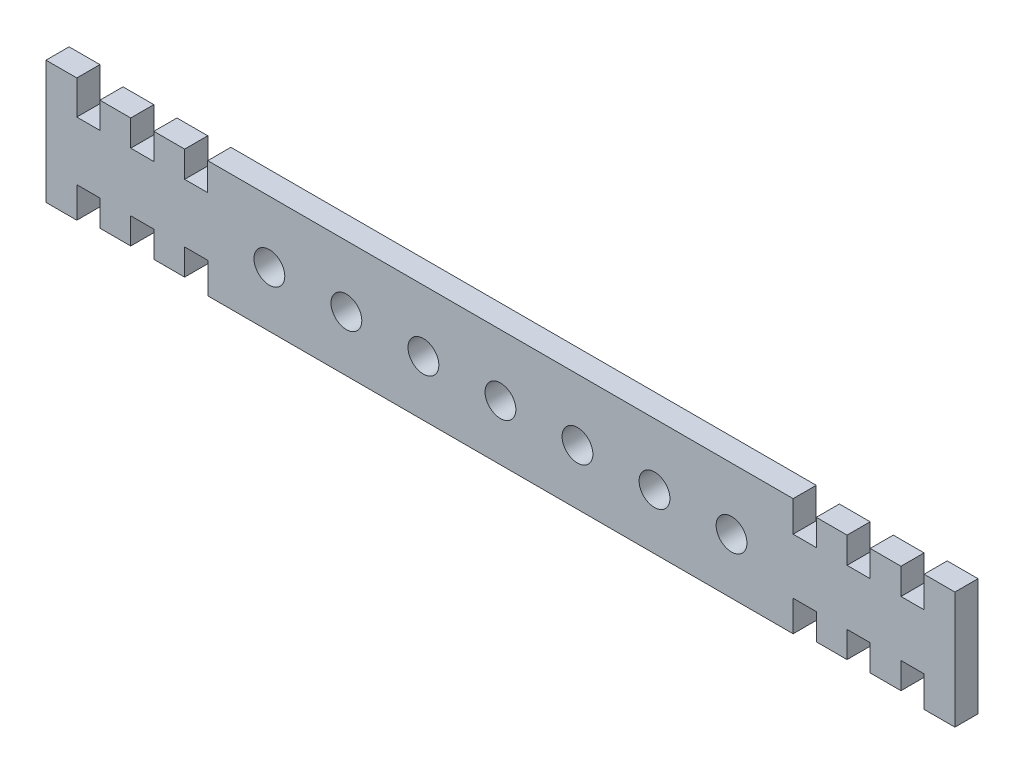
SolidWorks part; units mm, degrees
ref_plane "前视基准面" through (0, 0, 0) normal (0, 0, 1) x (1, 0, 0)
ref_plane "上视基准面" through (0, 0, 0) normal (0, 1, 0) x (1, 0, 0)
ref_plane "右视基准面" through (0, 0, 0) normal (1, 0, 0) x (0, 0, -1)
other "Configuration Table"
sketch "草图1" plane through (0, 0, 0) normal (0, 0, 1) x (1, 0, 0)
  line L0 (0, 0) -> (27.0318, 0) construction
  line L1 (0, -1.1987) -> (0, -17.6851) construction
  line L2 (-19.0005, 4) -> (18.9995, 4)
  line L37 (-19.0005, 4) -> (-19.0005, 2.2)
  line L38 (18.9995, 4) -> (18.9995, 2)
  line L39 (18.9995, 2) -> (20.5, 2)
  line L40 (20.5, 2) -> (20.5, 3.7)
  line L41 (20.5, 3.7) -> (22.4996, 3.7)
  line L42 (22.4996, 3.7) -> (22.4996, 2)
  line L43 (22.4996, 2) -> (24.0001, 2)
  line L44 (24.0001, 2) -> (24.0001, 3.7)
  line L45 (24.0001, 3.7) -> (25.9996, 3.7)
  line L46 (25.9996, 3.7) -> (25.9996, 2)
  line L48 (25.9996, 2) -> (27.5001, 2)
  line L49 (27.5001, 2) -> (27.5001, 4)
  line L50 (27.5001, 4) -> (29.4997, 4)
  line L51 (29.4997, 4) -> (29.4997, -3.6)
  line L54 (27.5, -3.6) -> (29.4997, -3.6)
  line L55 (27.5, -1.6) -> (27.5, -3.6)
  line L56 (26, -1.6) -> (27.5, -1.6)
  line L57 (26, -3.3) -> (26, -1.6)
  line L58 (24, -3.3) -> (26, -3.3)
  line L59 (24, -1.6) -> (24, -3.3)
  line L60 (22.5, -1.6) -> (24, -1.6)
  line L61 (22.5, -3.3) -> (22.5, -1.6)
  line L62 (20.5, -3.3) -> (22.5, -3.3)
  line L63 (20.5, -1.6) -> (20.5, -3.3)
  line L64 (19, -1.6) -> (20.5, -1.6)
  line L65 (19, -3.6) -> (19, -1.6)
  line L66 (-19, -3.6) -> (-19, -1.6)
  line L67 (-19, -1.6) -> (-20.5, -1.6)
  line L68 (-20.5, -1.6) -> (-20.5, -3.3)
  line L69 (-20.5, -3.3) -> (-22.5, -3.3)
  line L70 (-22.5, -3.3) -> (-22.5, -1.6)
  line L71 (-22.5, -1.6) -> (-24, -1.6)
  line L72 (-24, -1.6) -> (-24, -3.3)
  line L73 (-24, -3.3) -> (-26, -3.3)
  line L74 (-26, -3.3) -> (-26, -1.6)
  line L75 (-26, -1.6) -> (-27.5, -1.6)
  line L76 (-27.5, -1.6) -> (-27.5, -3.6)
  line L77 (-27.5, -3.6) -> (-29.5, -3.6)
  line L78 (-29.5, 4.4) -> (-29.5, -3.6)
  line L79 (-27.5, 4.4) -> (-29.5, 4.4)
  line L80 (-27.5, 2.2) -> (-27.5, 4.4)
  line L81 (-26, 2.2) -> (-27.5, 2.2)
  line L82 (-26, 3.9) -> (-26, 2.2)
  line L83 (-24, 3.9) -> (-26, 3.9)
  line L84 (-24, 2.2) -> (-24, 3.9)
  line L85 (-22.5, 2.2) -> (-24, 2.2)
  line L86 (-22.5, 3.9) -> (-22.5, 2.2)
  line L87 (-20.5, 3.9) -> (-22.5, 3.9)
  line L88 (-20.5, 2.2) -> (-20.5, 3.9)
  line L89 (-19.0005, 2.2) -> (-20.5, 2.2)
  line L91 (-19, -3.6) -> (19, -3.6)
  circle A0 centre (0, 0) radius 1
  circle A1 centre (5, 0) radius 1
  circle A2 centre (10, 0) radius 1
  circle A3 centre (15, 0) radius 1
  circle A5 centre (-5, 0) radius 1
  circle A6 centre (-10, 0) radius 1
  circle A7 centre (-15, 0) radius 1
  arc A9 (19, 0) -> (21, 0) centre (20, 0) ccw [skipped]
  arc A10 (-21, 0) -> (-19, 0) centre (-20, 0) ccw [skipped]
  point P6 (0, -4)
  point P43 (0, 4)
  dimension "D2" = 38
  dimension "D3" = 52
  dimension "D4" = 45
  dimension "D5" = 1.7
  dimension "D6" = 1.7
  dimension "D15" = 5
  dimension "D16" = 5
extrude "凸台-拉伸1" add sketch "草图1" along normal blind 1.5
